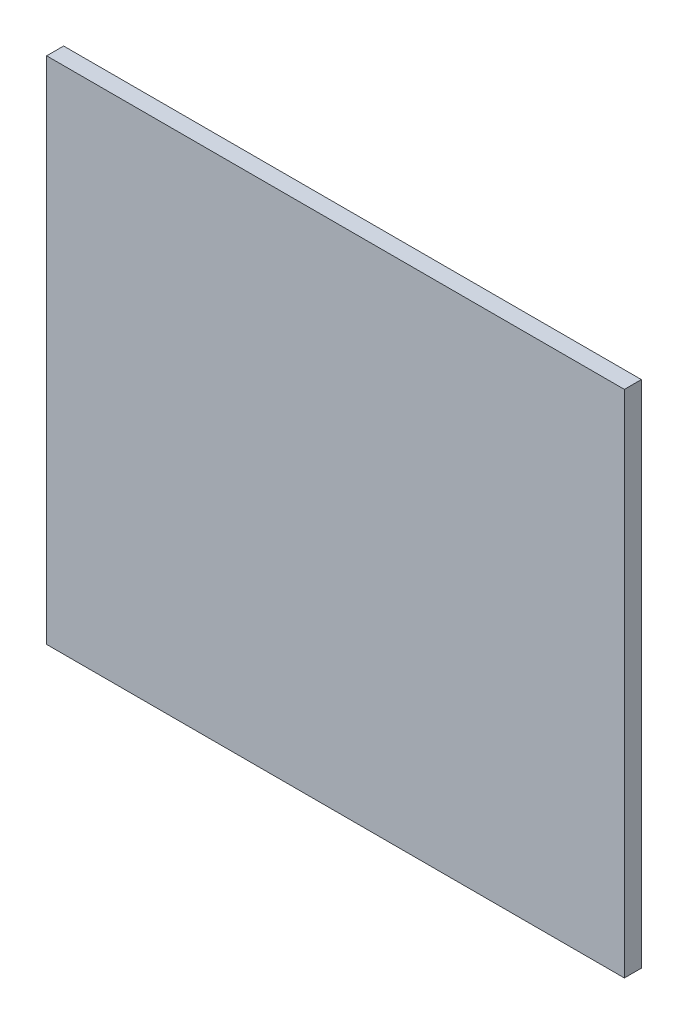
SolidWorks part; units mm, degrees
ref_plane "Front Plane" through (0, 0, 0) normal (0, 0, 1) x (1, 0, 0)
ref_plane "Top Plane" through (0, 0, 0) normal (0, 1, 0) x (1, 0, 0)
ref_plane "Right Plane" through (0, 0, 0) normal (1, 0, 0) x (0, 0, -1)
sketch "Sketch2" plane through (0, 0, 0) normal (0, 0, 1) x (1, 0, 0)
  line L1 (-85, 75) -> (85, 75)
  line L2 (-85, 75) -> (-85, -75)
  line L3 (-85, -75) -> (85, -75)
  line L4 (85, 75) -> (85, -75)
  line L5 (-85, 75) -> (85, -75) construction
  line L6 (-85, -75) -> (85, 75) construction
  point P0 (0, 0)
  dimension "D1" = 170
  dimension "D2" = 150
extrude "Boss-Extrude1" add sketch "Sketch2" along normal blind 5
